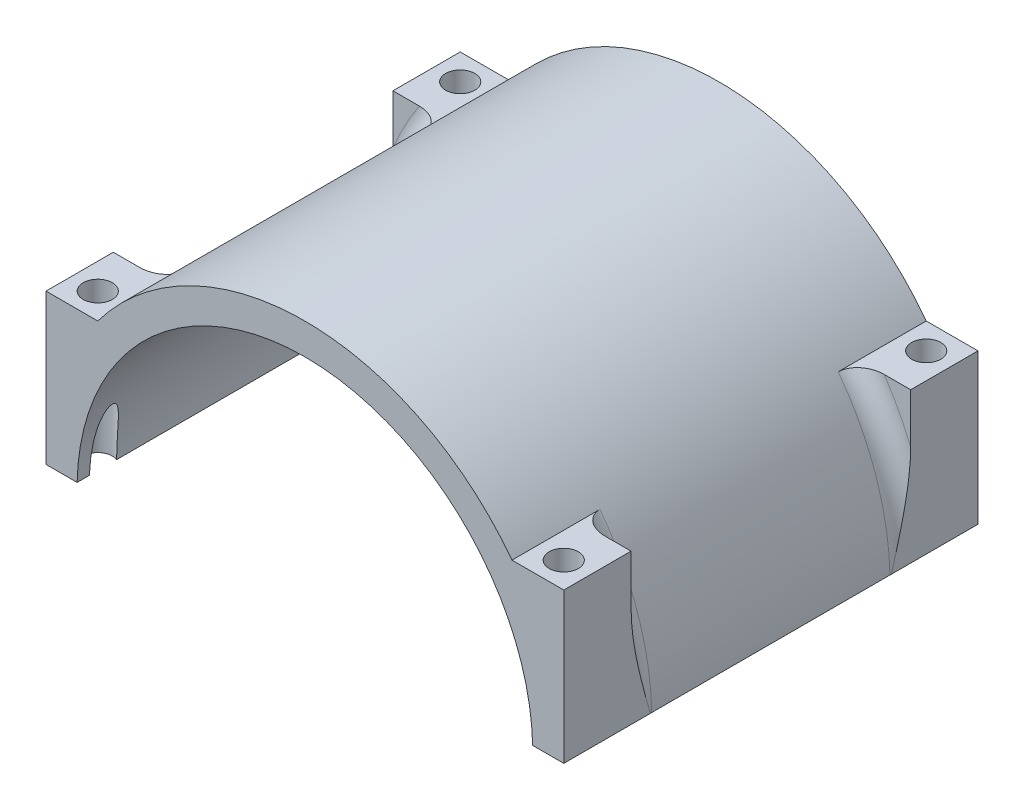
SolidWorks part; units mm, degrees
material "ABS"
ref_plane "Front Plane" through (0, 0, 0) normal (0, 0, 1) x (1, 0, 0)
ref_plane "Top Plane" through (0, 0, 0) normal (0, 1, 0) x (1, 0, 0)
ref_plane "Right Plane" through (0, 0, 0) normal (1, 0, 0) x (0, 0, -1)
sketch "Sketch1" plane through (0, 0, 0) normal (0, 0, 1) x (1, 0, 0)
  line L0 (55.88, 0) -> (63.5, 0)
  line L1 (-63.5, 0) -> (-55.88, 0)
  arc A0 (55.88, 0) -> (-55.88, 0) centre (0, 0) ccw
  arc A1 (63.5, 0) -> (-63.5, 0) centre (0, 0) ccw
  dimension "D1" = 55.88
  dimension "D2" = 7.62
extrude "Boss-Extrude1" add sketch "Sketch1" along normal mid plane 101.6
sketch "Sketch2" plane through (0, 0, -50.8) normal (0, 0, -1) x (-1, 0, 0)
  line L0 (0, 0) -> (0, 55.88) construction
  line L1 (-63.5, 0) -> (-63.5, 38.1)
  line L2 (55.88, 0) -> (63.5, 0)
  line L3 (-63.5, 0) -> (-55.88, 0)
  line L4 (55.88, 0) -> (63.5, 0)
  line L5 (-63.5, 0) -> (-55.88, 0)
  line L6 (-63.5, 38.1) -> (-50.8, 38.1)
  line L7 (63.5, 38.1) -> (50.8, 38.1)
  line L8 (63.5, 0) -> (55.88, 0)
  line L9 (63.5, 0) -> (63.5, 38.1)
  arc A0 (55.88, 0) -> (-55.88, 0) centre (0, 0) ccw construction
  arc A2 (55.88, 0) -> (-55.88, 0) centre (0, 0) ccw
  arc A3 (63.5, 0) -> (-63.5, 0) centre (0, 0) ccw
  arc A4 (55.88, 0) -> (-55.88, 0) centre (0, 0) ccw
  arc A5 (63.5, 0) -> (-63.5, 0) centre (0, 0) ccw
  arc M8 (63.5, 0) -> (-63.5, 0) centre (0, 0) ccw
  dimension "D2" = 12.7
extrude "Boss-Extrude2" add sketch "Sketch2" against normal blind 16.51 contours L6 L1 M8 | L9 L7 M8
mirror "Mirror1" about plane through (0, 0, 0) normal (0, 0, 1) of "Boss-Extrude2"
sketch "Sketch4" plane through (0, 0, 50.8) normal (0, 0, 1) x (1, 0, 0)
  line L0 (-63.5, 0) -> (-63.5, 38.1) construction
  line L1 (63.5, 0) -> (-63.5, 0)
  line L2 (63.5, 0) -> (63.5, 1.27)
  line L3 (63.5, 1.27) -> (-63.5, 1.27)
  line L4 (-63.5, 0) -> (-63.5, 1.27)
  dimension "D1" = 1.27
extrude "Cut-Extrude1" cut sketch "Sketch4" against normal through all
sketch "Sketch5" plane through (0, 38.1, 0) normal (0, 1, 0) x (1, 0, 0)
  line L0 (0, 50.8) -> (0, -50.8) construction
  line L1 (50.8, 50.8) -> (-50.8, 50.8) construction
  line L2 (-50.8, -50.8) -> (50.8, -50.8) construction
  line L3 (-63.4873, 0) -> (63.4873, 0) construction
  line L4 (-63.4873, 34.29) -> (-63.4873, -34.29) construction
  line L5 (63.4873, -34.29) -> (63.4873, 34.29) construction
  point P5 (-57.15, 44.45)
  point P20 (57.15, 44.45)
  point P22 (57.15, -44.45)
  point P23 (-57.15, -44.45)
  dimension "D1" = 57.15
  dimension "D2" = 44.45
hole_wizard "1/4 Clearance Hole1" positions "3DSketch1" profile "Sketch6" hole size "1/4" standard "ANSI Inch" end condition through all
sketch3d "3DSketch1"
  point P12 (-57.15, 38.1, -44.45)
  point P15 (57.15, 38.1, -44.45)
  point P18 (-57.15, 38.1, 44.45)
  point P21 (57.15, 38.1, 44.45)
sketch "Sketch6" plane through (-57.15, 38.1, -44.45) normal (1, 0, 0) x (0, 0, 1)
  line L0 (0, 0) -> (0, 36.83)
  line L1 (0, 36.83) -> (3.5712, 36.83)
  line L2 (3.5712, 36.83) -> (3.5712, 0)
  line L5 (3.5712, 0) -> (0, 0)
  line L11 (0, -6.35) -> (0, 107.95) construction
  dimension "Thru Hole Dia." = 7.1425
  dimension "Thru Hole Depth" = 36.83
fillet "Fillet1" radius 5.08 4 edges at (60.0376, 20.6819, 34.29) (-60.0376, 20.6819, 34.29) (-60.0376, 20.6819, -34.29) (60.0376, 20.6819, -34.29)
equation "\"radial offset\"= .2in"
equation "\"radial thickness\"= .3in"
equation "\"length\"= 4in"
equation "\"D1@Sketch1\"=\"radial offset\"+2"
equation "\"D2@Sketch1\"=\"radial thickness\""
equation "\"D1@Boss-Extrude1\"=\"length\""
equation "\"platform width\"=0.5in'Controls the width of the platform that the mating screws and nuts sits on"
equation "\"D2@Sketch2\"=\"platform width\""
equation "\"vertical gap\"=0.1in'Gap between mating surfaces to increase tension"
equation "\"D1@Sketch4\"=\"vertical gap\"/2"
equation "\"platform fillet\"=.2in"
equation "\"D1@Fillet1\"=\"platform fillet\""
